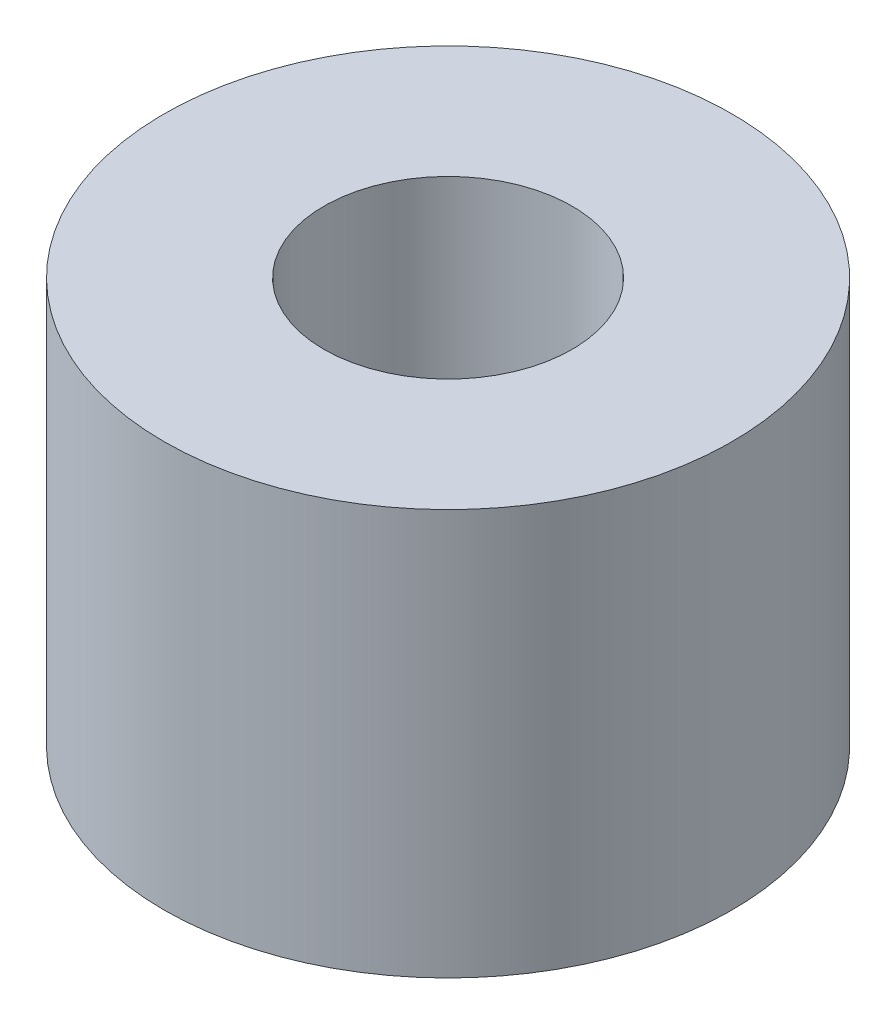
SolidWorks part; units mm, degrees
ref_plane "Alzado" through (0, 0, 0) normal (0, 0, 1) x (1, 0, 0)
ref_plane "Planta" through (0, 0, 0) normal (0, 1, 0) x (1, 0, 0)
ref_plane "Vista lateral" through (0, 0, 0) normal (1, 0, 0) x (0, 0, -1)
sketch "Croquis1" plane through (0, 0, 0) normal (0, 1, 0) x (1, 0, 0)
  circle A0 centre (0, 0) radius 3.5
  circle A1 centre (0, 0) radius 1.53
  dimension "D1" = 3.06
  dimension "D2" = 7
extrude "Saliente-Extruir1" add sketch "Croquis1" along normal blind 5
